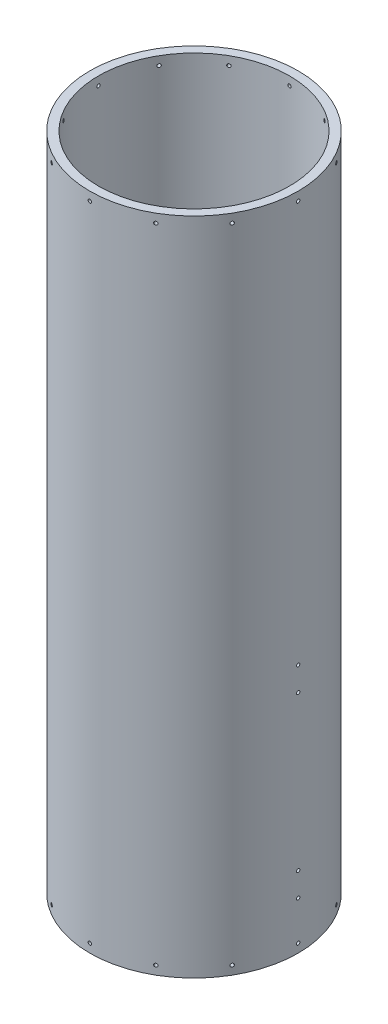
SolidWorks part; units mm, degrees
ref_plane "Front Plane" through (0, 0, 0) normal (0, 0, 1) x (1, 0, 0)
ref_plane "Top Plane" through (0, 0, 0) normal (0, 1, 0) x (1, 0, 0)
ref_plane "Right Plane" through (0, 0, 0) normal (1, 0, 0) x (0, 0, -1)
sketch "Sketch1" plane through (0, 0, 0) normal (0, 1, 0) x (1, 0, 0)
  circle A0 centre (0, 0) radius 152.4
  circle A1 centre (0, 0) radius 139.7
  dimension "D2" = 304.8
  dimension "D1" = 279.4
extrude "Boss-Extrude1" add sketch "Sketch1" along normal blind 965.2
ref_plane "Plane1" through (-152.4, 0, 0) normal (-1, 0, 0) x (0, 0, 1)
hole_wizard "#10 (0.1935) Diameter Hole1" positions "Sketch2" profile "Sketch3" hole size "#10" standard "ANSI Inch"
sketch "Sketch2" plane through (-152.4, 0, 0) normal (-1, 0, 0) x (0, 0, 1)
  line L0 (0, -167.64) -> (0, 167.64) construction
  line L1 (152.4, 965.2) -> (-152.4, 965.2) construction
  point P0 (0, 952.5)
  dimension "D1" = 12.7
sketch "Sketch3" plane through (-152.4, 952.5, 0) normal (0, 1, 0) x (0, 0, 1)
  line L0 (0, 0) -> (0, 343.2351)
  line L1 (0, 343.2351) -> (2.4574, 343.2351)
  line L2 (2.4574, 343.2351) -> (2.4574, 0)
  line L5 (2.4574, 0) -> (0, 0)
  line L11 (0, -6.35) -> (0, 107.95) construction
  dimension "Thru Hole Dia." = 4.9149
  dimension "Thru Hole Depth" = 343.2351
pattern_circular "CirPattern1" count 12 over 360 about axis through (0, 965.2, 0) along (0, 1, 0) of "#10 (0.1935) Diameter Hole1"
ref_plane "Plane2" through (0, 482.6, 0) normal (0, 1, 0) x (1, 0, 0)
mirror "Mirror1" about plane through (0, 482.6, 0) normal (0, 1, 0) of "CirPattern1", "#10 (0.1935) Diameter Hole1"
hole_wizard "#10 (0.1935) Diameter Hole2" positions "Sketch7" profile "Sketch8" hole size "#10" standard "ANSI Inch"
sketch "Sketch7" plane through (-152.4, 0, 0) normal (-1, 0, 0) x (0, 0, 1)
  line L0 (0, 365.125) -> (0, 330.2)
  line L1 (0, 330.2) -> (0, 0)
  point P0 (0, 365.125)
  point P2 (0, 330.2)
  point P11 (0, 104.775)
  point P13 (0, 69.85)
  dimension "D1" = 34.925
  dimension "D2" = 330.2
  dimension "D3" = 34.925
  dimension "D4" = 260.35
sketch "Sketch8" plane through (-152.4, 365.125, 0) normal (0, 1, 0) x (0, 0, 1)
  line L0 (0, 0) -> (0, 304.8)
  line L1 (0, 304.8) -> (2.4574, 304.8)
  line L2 (2.4574, 304.8) -> (2.4574, 0)
  line L5 (2.4574, 0) -> (0, 0)
  line L11 (0, -6.35) -> (0, 107.95) construction
  dimension "Thru Hole Dia." = 4.9149
  dimension "Thru Hole Depth" = 304.8
pattern_circular "CirPattern2" count 2 over 360 about axis through (0, 965.2, 0) along (0, 1, 0) of "#10 (0.1935) Diameter Hole2"
